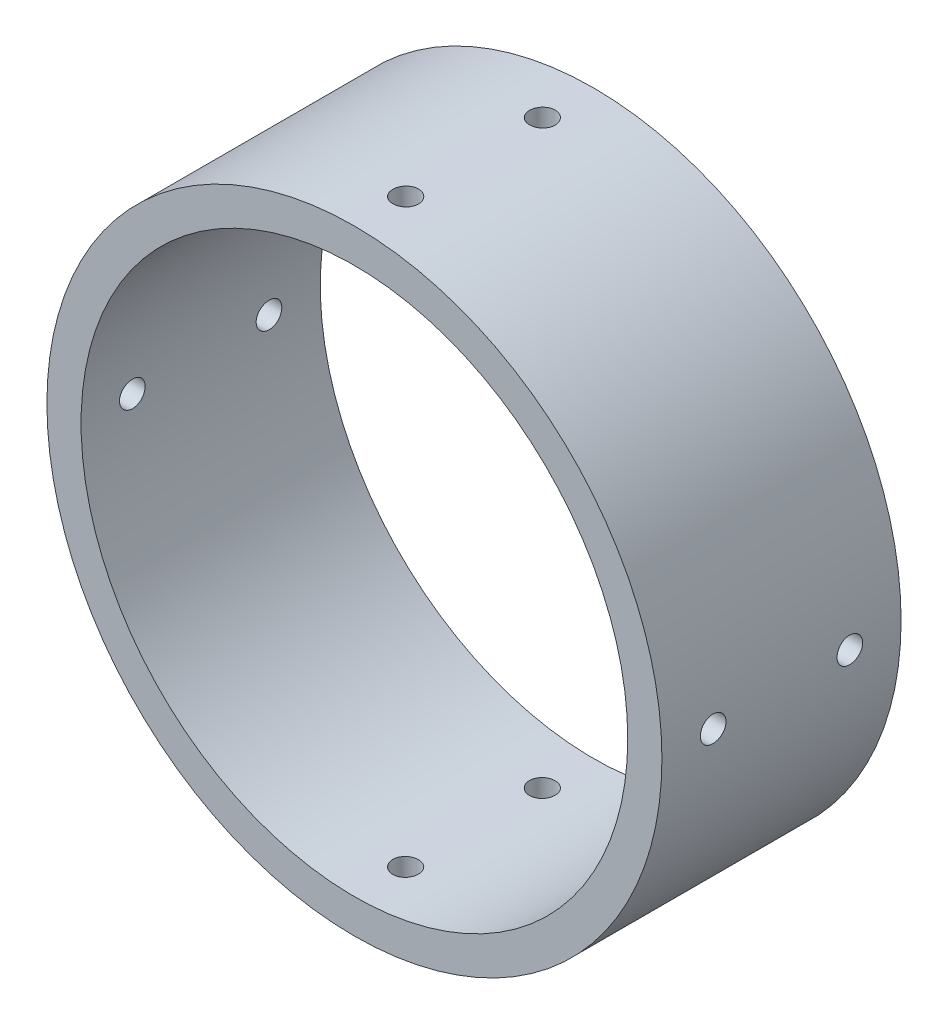
SolidWorks part; units mm, degrees
material "PET"
ref_plane "Front Plane" through (0, 0, 0) normal (0, 0, 1) x (1, 0, 0)
ref_plane "Top Plane" through (0, 0, 0) normal (0, 1, 0) x (1, 0, 0)
ref_plane "Right Plane" through (0, 0, 0) normal (1, 0, 0) x (0, 0, -1)
sketch "Sketch1" plane through (0, 0, 0) normal (0, 0, 1) x (1, 0, 0)
  circle A0 centre (0, 0) radius 18
  circle A1 centre (0, 0) radius 16
  dimension "D1" = 36
  dimension "D2" = 2
extrude "Boss-Extrude1" add sketch "Sketch1" along normal blind 14
ref_plane "Plane1" through (0, 0, 7) normal (0, 0, 1) x (1, 0, 0)
ref_plane "Plane2" through (0, 18, 0) normal (0, 1, 0) x (1, 0, 0)
sketch "Sketch2" plane through (0, 18, 0) normal (0, 1, 0) x (1, 0, 0)
  line L0 (0, -3) -> (0, -11)
  circle A0 centre (0, -3) radius 0.75
  circle A1 centre (0, -11) radius 0.75
  point P3 (0, -7)
  dimension "D3" = 1.5
  dimension "D4" = 1.5
  dimension "D1" = 8
  dimension "D2" = 7
extrude "Cut-Extrude1" cut sketch "Sketch2" against normal blind 5
pattern_circular "CirPattern1" count 4 over 360 about axis through (0, 0, 14) along (0, 0, 1) of "Cut-Extrude1"
